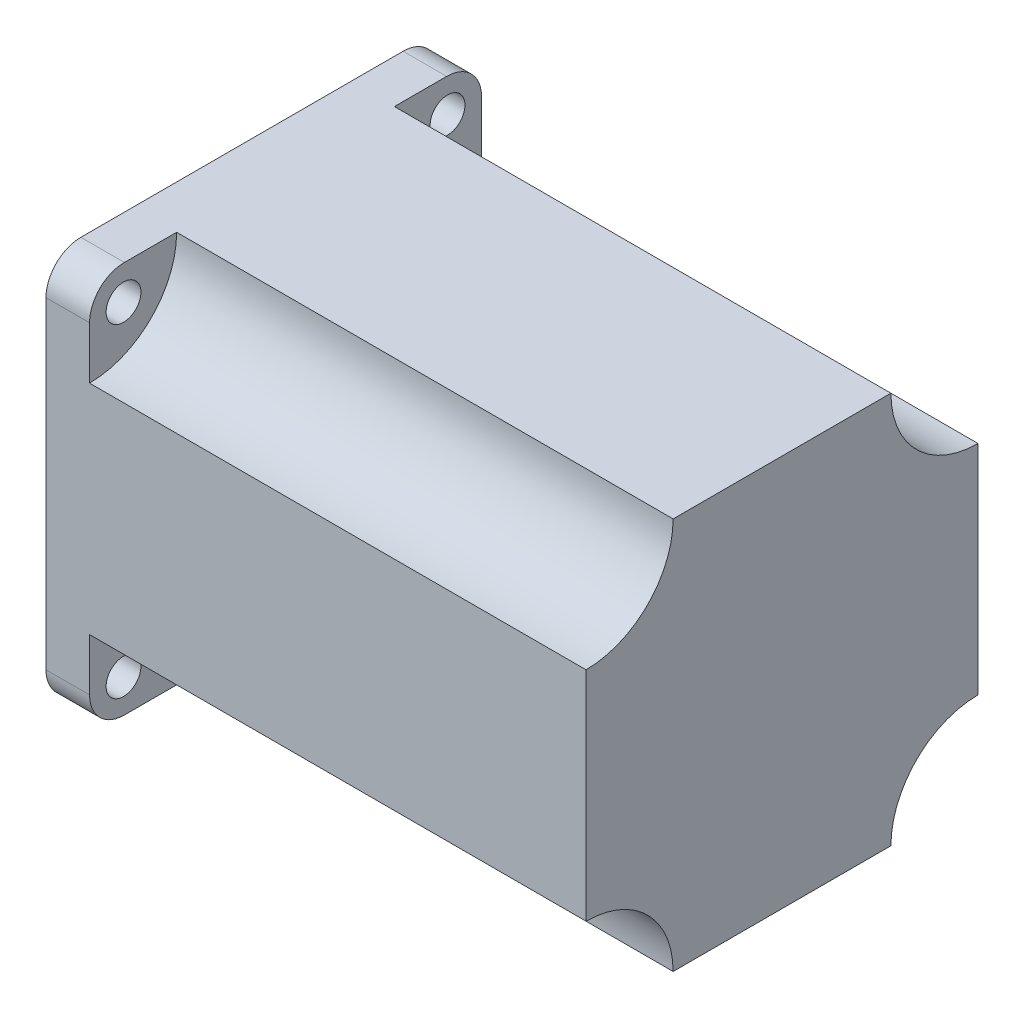
SolidWorks part; units mm, degrees
material "Plain Carbon Steel"
ref_plane "Front Plane" through (0, 0, 0) normal (0, 0, 1) x (1, 0, 0)
ref_plane "Top Plane" through (0, 0, 0) normal (0, 1, 0) x (1, 0, 0)
ref_plane "Right Plane" through (0, 0, 0) normal (1, 0, 0) x (0, 0, -1)
sketch "Sketch1" plane through (0, 0, 0) normal (1, 0, 0) x (0, 0, -1)
  line L0 (23.622, 23.622) -> (-23.622, 23.622) construction
  line L1 (28.575, 28.575) -> (-28.575, 28.575)
  line L2 (28.575, 28.575) -> (28.575, -28.575)
  line L3 (28.575, -28.575) -> (-28.575, -28.575)
  line L4 (-28.575, 28.575) -> (-28.575, -28.575)
  line L5 (28.575, 28.575) -> (-28.575, -28.575) construction
  line L6 (28.575, -28.575) -> (-28.575, 28.575) construction
  line L7 (-23.622, 23.622) -> (-23.622, -23.622) construction
  line L8 (-23.622, -23.622) -> (23.622, -23.622) construction
  line L9 (23.622, -23.622) -> (23.622, 23.622) construction
  circle A0 centre (23.622, 23.622) radius 2.54
  circle A1 centre (-23.622, 23.622) radius 2.54
  circle A2 centre (-23.622, -23.622) radius 2.54
  circle A3 centre (23.622, -23.622) radius 2.54
  point P0 (0, 0)
  dimension "D2" = 57.15
  dimension "D3" = 5.08
  dimension "D1" = 47.244
extrude "Boss-Extrude1" add sketch "Sketch1" along normal blind 6.35
fillet "Fillet1" radius 5.08 4 edges at (3.175, -28.575, -28.575) (3.175, -28.575, 28.575) (3.175, 28.575, -28.575) (3.175, 28.575, 28.575)
sketch "Sketch5" plane through (0, 0, 0) normal (-1, 0, 0) x (0, 0, 1)
  circle A0 centre (0, 0) radius 19.05
  dimension "D1" = 38.1
extrude "Boss-Extrude4" add sketch "Sketch5" along normal blind 1.524
sketch "Sketch6" plane through (-1.524, 0, 0) normal (-1, 0, 0) x (0, 0, 1)
  circle A0 centre (0, 0) radius 3.175
  dimension "D1" = 6.35
extrude "Boss-Extrude5" add sketch "Sketch6" along normal blind 19.05
sketch "Sketch7" plane through (6.35, 0, 0) normal (1, 0, 0) x (0, 0, -1)
  line L0 (-23.495, -28.575) -> (23.495, -28.575) construction
  line L1 (-28.575, 28.575) -> (28.575, 28.575) construction
  line L2 (-28.575, 28.575) -> (-28.575, -28.575) construction
  line L3 (-28.575, -28.575) -> (28.575, -28.575) construction
  line L4 (28.575, 28.575) -> (28.575, -28.575) construction
  line L5 (-28.575, 28.575) -> (28.575, -28.575) construction
  line L6 (-28.575, -28.575) -> (28.575, 28.575) construction
  line L7 (-28.575, 23.495) -> (-28.575, -23.495) construction
  line L8 (-15.875, 28.575) -> (15.875, 28.575)
  line L9 (28.575, 15.875) -> (28.575, -15.875)
  line L10 (15.875, -28.575) -> (-15.875, -28.575)
  line L11 (-28.575, -15.875) -> (-28.575, 15.875)
  arc A0 (-28.575, 15.875) -> (-15.875, 28.575) centre (-28.575, 28.575) ccw
  arc A1 (15.875, 28.575) -> (28.575, 15.875) centre (28.575, 28.575) ccw
  arc A2 (28.575, -15.875) -> (15.875, -28.575) centre (28.575, -28.575) ccw
  arc A3 (-15.875, -28.575) -> (-28.575, -15.875) centre (-28.575, -28.575) ccw
  point P0 (0, 0)
  dimension "D1" = 25.4
extrude "Boss-Extrude6" add sketch "Sketch7" along normal blind 72.39 contours A0 L8 A1 L9 A2 L10 A3 L11
